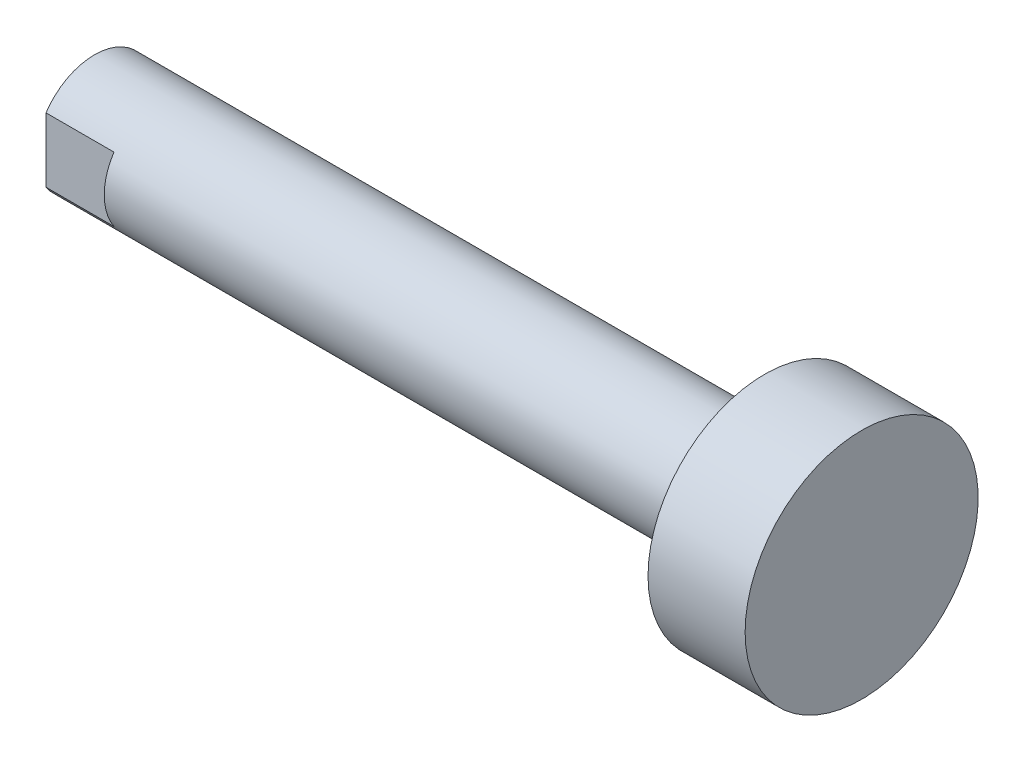
SolidWorks part; units mm, degrees
ref_plane "Front Plane" through (0, 0, 0) normal (0, 0, 1) x (1, 0, 0)
ref_plane "Top Plane" through (0, 0, 0) normal (0, 1, 0) x (1, 0, 0)
ref_plane "Right Plane" through (0, 0, 0) normal (1, 0, 0) x (0, 0, -1)
ref_plane "Plane1" through (0, 0, 0) normal (0, 0, -1) x (-1, 0, 0)
sketch "Sketch1" plane through (0, 0, 0) normal (0, 0, -1) x (-1, 0, 0)
  line L0 (-36, 6) -> (-36, 0)
  line L1 (-36, 0) -> (-31, 0)
  line L2 (-31, 0) -> (-31, 6)
  line L3 (-31, 6) -> (-36, 6)
  line L4 (-36, 0) -> (-31, 0) construction
revolve "Revolve1" add sketch "Sketch1" angle 360 about L4
sketch "Sketch2" plane through (31, 0, 0) normal (-1, 0, 0) x (0, 0, 1)
  circle A0 centre (0, 0) radius 3
extrude "Boss-Extrude1" add sketch "Sketch2" along normal blind 34.5
sketch "Sketch3" plane through (-3.5, 0, 0) normal (-1, 0, 0) x (0, 0, 1)
  line L0 (-2.5, -1.6583) -> (-2.5, 1.6583)
  arc A0 (-2.5, 1.6583) -> (-2.5, -1.6583) centre (0, 0) ccw
extrude "Cut-Extrude1" cut sketch "Sketch3" against normal blind 3.5
sketch "Sketch4" plane through (-3.5, 0, 0) normal (-1, 0, 0) x (0, 0, 1)
  line L0 (2.5, 1.6583) -> (2.5, -1.6583)
  arc A0 (2.5, -1.6583) -> (2.5, 1.6583) centre (0, 0) ccw
extrude "Cut-Extrude2" cut sketch "Sketch4" against normal blind 3.5
hole_wizard "M2 Clearance Hole1" positions "Sketch6" profile "Sketch5" hole size "M2" standard "ANSI Metric"
sketch "Sketch6" plane through (-3.5, 0, 0) normal (-1, 0, 0) x (0, 0, 1)
  point P0 (0, 0)
sketch "Sketch5" plane through (-3.5, 0, 0) normal (0, 1, 0) x (0, 0, 1)
  line L0 (0, 0) -> (0, 6.7099)
  line L1 (0, 6.7099) -> (1.2295, 6)
  line L2 (1.2295, 6) -> (1.2295, 0)
  line L5 (1.2295, 0) -> (0, 0)
  line L10 (0, 6.7099) -> (-1.2295, 6) construction
  line L11 (0, -6.35) -> (0, 107.95) construction
  dimension "Hole Dia." = 2.459
  dimension "Hole Depth" = 6
  dimension "Drill Angle" = 120
chamfer "Chamfer1" distance 0.2705 angle 45 1 edges at (-3.5, 0, 1.2295)
